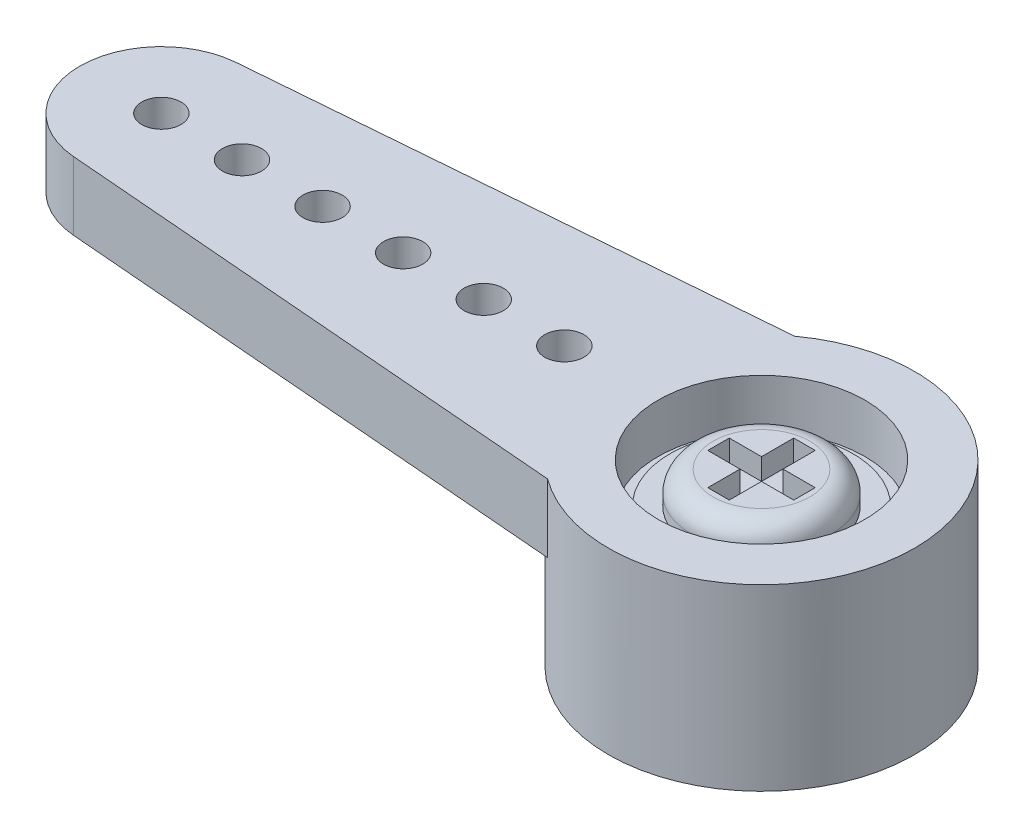
SolidWorks part; units mm, degrees
material "Nylon 101"
ref_plane "Front Plane" through (0, 0, 0) normal (0, 0, 1) x (1, 0, 0)
ref_plane "Top Plane" through (0, 0, 0) normal (0, 1, 0) x (1, 0, 0)
ref_plane "Right Plane" through (0, 0, 0) normal (1, 0, 0) x (0, 0, -1)
sketch "Sketch18" plane through (0, 0, 0) normal (0, 1, 0) x (1, 0, 0)
  line L0 (-16.1163, 0) -> (3.6195, 0) construction
  line L1 (-14.3431, 1.924) -> (-2.1374, 2.921)
  line L2 (-14.3431, -1.924) -> (-2.1374, -2.921)
  arc A0 (-2.1374, -2.921) -> (-2.1374, 2.921) centre (0, 0) ccw
  arc A1 (-14.3431, 1.924) -> (-14.3431, -1.924) centre (-14.1859, 0) ccw
  dimension "D1" = 1.9304
  dimension "D2" = 3.6195
  dimension "D3" = 19.7358
  dimension "D4" = 5.842
extrude "Extrude17" add sketch "Sketch18" along normal blind 1.6129
sketch "Sketch19" plane through (0, 1.6129, 0) normal (0, 1, 0) x (1, 0, 0)
  circle A0 centre (0, 0) radius 3.6195
  arc A1 (-2.1374, -2.921) -> (-2.1374, 2.921) centre (0, 0) ccw construction
extrude "Extrude19" add sketch "Sketch19" against normal blind 4.2291
sketch "Sketch20" plane through (0, 1.6129, 0) normal (0, 1, 0) x (1, 0, 0)
  line L0 (-14.1859, 0) -> (-12.2809, 0) construction
  line L1 (-12.2809, 0) -> (-10.3759, 0) construction
  line L2 (-10.3759, 0) -> (-8.4709, 0) construction
  line L3 (-8.4709, 0) -> (-6.5659, 0) construction
  line L4 (-6.5659, 0) -> (-4.6609, 0) construction
  line L5 (-4.6609, 0) -> (-2.7559, 0) construction
  line L6 (-2.7559, 0) -> (0, 0) construction
  circle A0 centre (-14.1859, 0) radius 0.4636
  circle A1 centre (0, 0) radius 1.27
  circle A3 centre (-4.6609, 0) radius 0.4636
  circle A4 centre (-6.5659, 0) radius 0.4636
  circle A5 centre (-8.4709, 0) radius 0.4636
  circle A6 centre (-10.3759, 0) radius 0.4636
  circle A7 centre (-12.2809, 0) radius 0.4636
  dimension "D1" = 0.9271
  dimension "D3" = 2.54
  dimension "D2" = 1.905
extrude "Extrude20" cut sketch "Sketch20" against normal through all
sketch "Sketch21" plane through (0, 1.6129, 0) normal (0, 1, 0) x (1, 0, 0)
  circle A0 centre (0, 0) radius 2.4447
  dimension "D1" = 4.8895
extrude "Extrude21" cut sketch "Sketch21" against normal blind 1.1557
sketch "Sketch22" plane through (0, -2.6162, 0) normal (0, -1, 0) x (1, 0, 0)
  circle A0 centre (0, 0) radius 2.286
  dimension "D1" = 4.572
extrude "Extrude22" cut sketch "Sketch22" against normal blind 2.3368
sketch "Sketch23" plane through (0, 0.4572, 0) normal (0, 1, 0) x (1, 0, 0)
  circle A0 centre (0, 0) radius 2.159
  dimension "D1" = 4.318
extrude "Extrude23" add sketch "Sketch23" along normal blind 0.2032 separate body
sketch "Sketch24" plane through (0, 0.6604, 0) normal (0, 1, 0) x (1, 0, 0)
  circle A0 centre (0, 0) radius 1.651
  dimension "D1" = 3.302
extrude "Extrude24" add sketch "Sketch24" along normal blind 0.762
sketch "Sketch25" plane through (0, 1.4224, 0) normal (0, 1, 0) x (1, 0, 0)
  line L0 (0, -1.651) -> (0, 1.651) construction
  line L1 (-1.651, 0) -> (1.651, 0) construction
  line L2 (0.254, -1.016) -> (-0.254, -1.016)
  line L3 (-0.254, -1.016) -> (-0.254, -0.254)
  line L4 (-0.254, -0.254) -> (-1.016, -0.254)
  line L5 (-1.016, -0.254) -> (-1.016, 0.254)
  line L6 (0.254, 1.016) -> (-0.254, 1.016)
  line L7 (-0.254, 1.016) -> (-0.254, 0.254)
  line L8 (-0.254, 0.254) -> (-1.016, 0.254)
  line L9 (0.254, 1.016) -> (0.254, 0.254)
  line L10 (0.254, -1.016) -> (0.254, -0.254)
  line L11 (0.254, -0.254) -> (1.016, -0.254)
  line L12 (1.016, -0.254) -> (1.016, 0.254)
  line L13 (0.254, 0.254) -> (1.016, 0.254)
  circle A0 centre (0, 0) radius 1.651 construction
  point P16 (-1.016, 0)
  point P17 (0, 1.016)
  point P19 (0, -1.016)
  dimension "D1" = 2.032
  dimension "D2" = 0.508
extrude "Extrude25" cut sketch "Sketch25" against normal blind 0.508
fillet "Fillet1" radius 0.508 1 edges at (0, 1.4224, 1.651)
